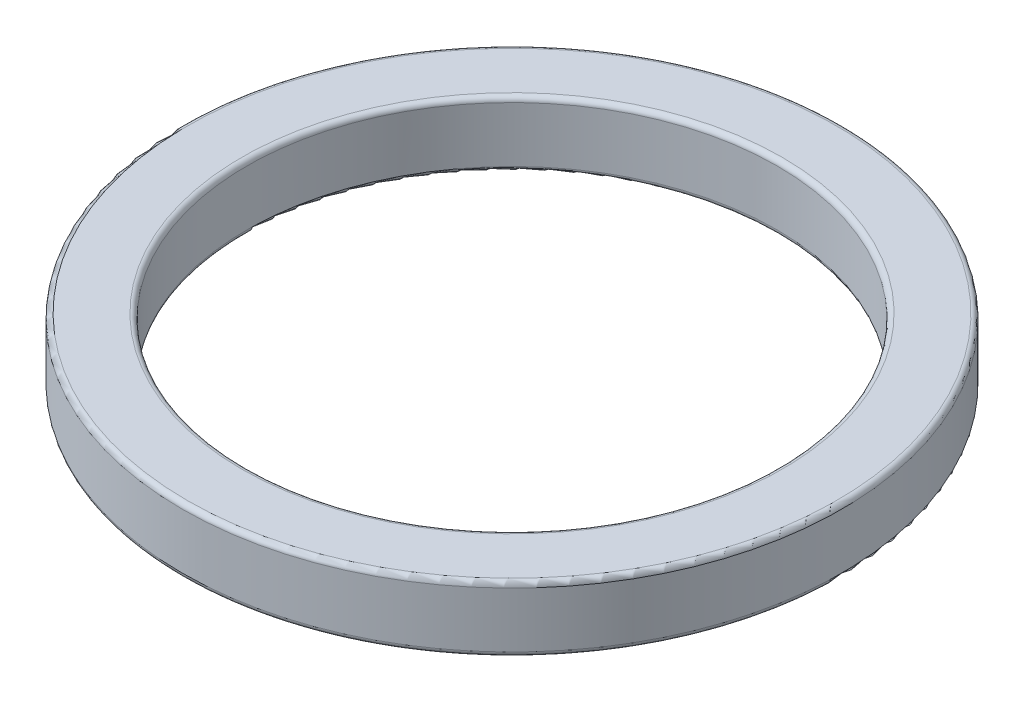
SolidWorks part; units mm, degrees
ref_plane "Plan de face" through (0, 0, 0) normal (0, 0, 1) x (1, 0, 0)
ref_plane "Plan de dessus" through (0, 0, 0) normal (0, 1, 0) x (1, 0, 0)
ref_plane "Plan de droite" through (0, 0, 0) normal (1, 0, 0) x (0, 0, -1)
sketch "Esquisse1" plane through (0, 0, 0) normal (0, 0, 1) x (1, 0, 0)
  line L0 (0, 0) -> (0, 4.3378) construction
  line L2 (5.27, 2.9717) -> (6.55, 2.9717)
  line L3 (5.27, 2.9717) -> (5.27, 1.6717)
  line L4 (5.27, 1.6717) -> (6.55, 1.6717)
  line L5 (6.55, 2.9717) -> (6.55, 1.6717)
  dimension "D1" = 13.1
  dimension "D2" = 10.54
  dimension "D3" = 1.3
revolve "Révolution1" add sketch "Esquisse1" angle 360 about L0
fillet "Congé1" radius 0.1 4 edges at (0, 2.9717, -5.27) (0, 2.9717, -6.55) (0, 1.6717, -6.55) (0, 1.6717, -5.27)
